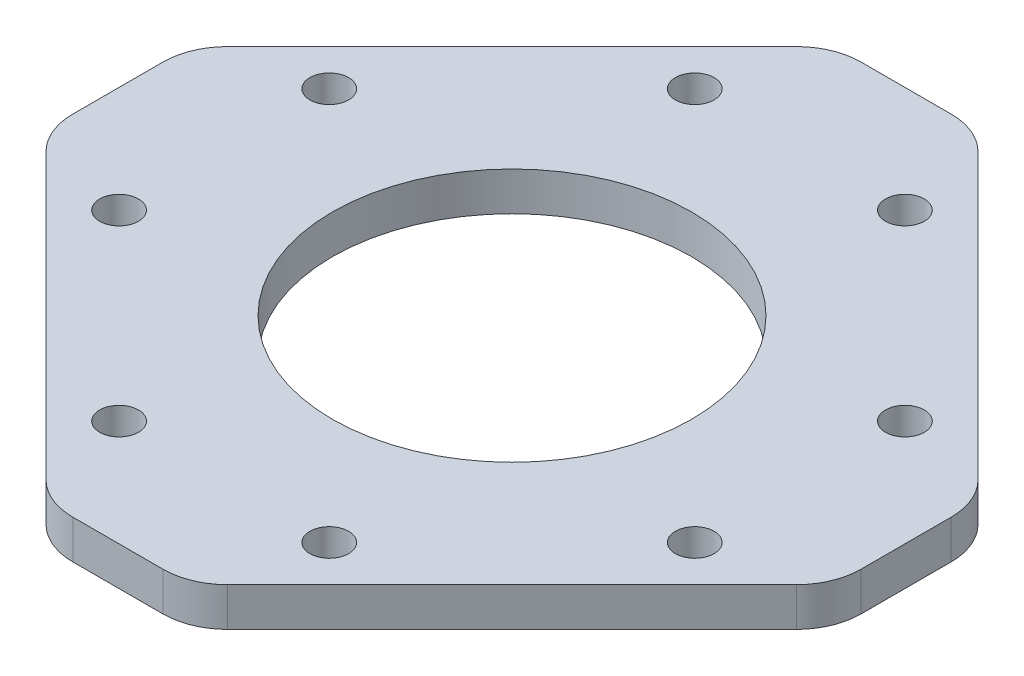
SolidWorks part; units mm, degrees
ref_plane "Front Plane" through (0, 0, 0) normal (0, 0, 1) x (1, 0, 0)
ref_plane "Top Plane" through (0, 0, 0) normal (0, 1, 0) x (1, 0, 0)
ref_plane "Right Plane" through (0, 0, 0) normal (1, 0, 0) x (0, 0, -1)
sketch "Sketch1" plane through (0, 0, 0) normal (0, 1, 0) x (1, 0, 0)
  line L0 (3.4914, 30.5) -> (-3.4914, 30.5)
  line L1 (-7.0269, 29.0355) -> (-29.0355, 7.0269)
  line L2 (-30.5, 3.4914) -> (-30.5, -3.4914)
  line L3 (-29.0355, -7.0269) -> (-7.0269, -29.0355)
  line L4 (-3.4914, -30.5) -> (3.4914, -30.5)
  line L5 (7.0269, -29.0355) -> (29.0355, -7.0269)
  line L6 (30.5, -3.4914) -> (30.5, 3.4914)
  line L7 (29.0355, 7.0269) -> (7.0269, 29.0355)
  arc A0 (7.0269, 29.0355) -> (3.4914, 30.5) centre (3.4914, 25.5) ccw
  arc A1 (-3.4914, 30.5) -> (-7.0269, 29.0355) centre (-3.4914, 25.5) ccw
  arc A2 (-29.0355, 7.0269) -> (-30.5, 3.4914) centre (-25.5, 3.4914) ccw
  arc A3 (-30.5, -3.4914) -> (-29.0355, -7.0269) centre (-25.5, -3.4914) ccw
  arc A4 (-7.0269, -29.0355) -> (-3.4914, -30.5) centre (-3.4914, -25.5) ccw
  arc A5 (3.4914, -30.5) -> (7.0269, -29.0355) centre (3.4914, -25.5) ccw
  arc A6 (29.0355, -7.0269) -> (30.5, -3.4914) centre (25.5, -3.4914) ccw
  arc A7 (30.5, 3.4914) -> (29.0355, 7.0269) centre (25.5, 3.4914) ccw
  circle A8 centre (-8.1317, -22.2739) radius 1.5
  circle A9 centre (8.1317, -22.2739) radius 1.5
  circle A10 centre (22.2739, -8.1317) radius 1.5
  circle A11 centre (22.2739, 8.1317) radius 1.5
  circle A12 centre (8.1317, 22.2739) radius 1.5
  circle A13 centre (-8.1317, 22.2739) radius 1.5
  circle A14 centre (-22.2739, -8.1317) radius 1.5
  circle A15 centre (-22.2739, 8.1317) radius 1.5
  circle A16 centre (0, 0) radius 13.9
  dimension "D1" = 27.8
  dimension "D2" = 31.1249
  dimension "D3" = 51
extrude "Boss-Extrude1" add sketch "Sketch1" along normal blind 3
